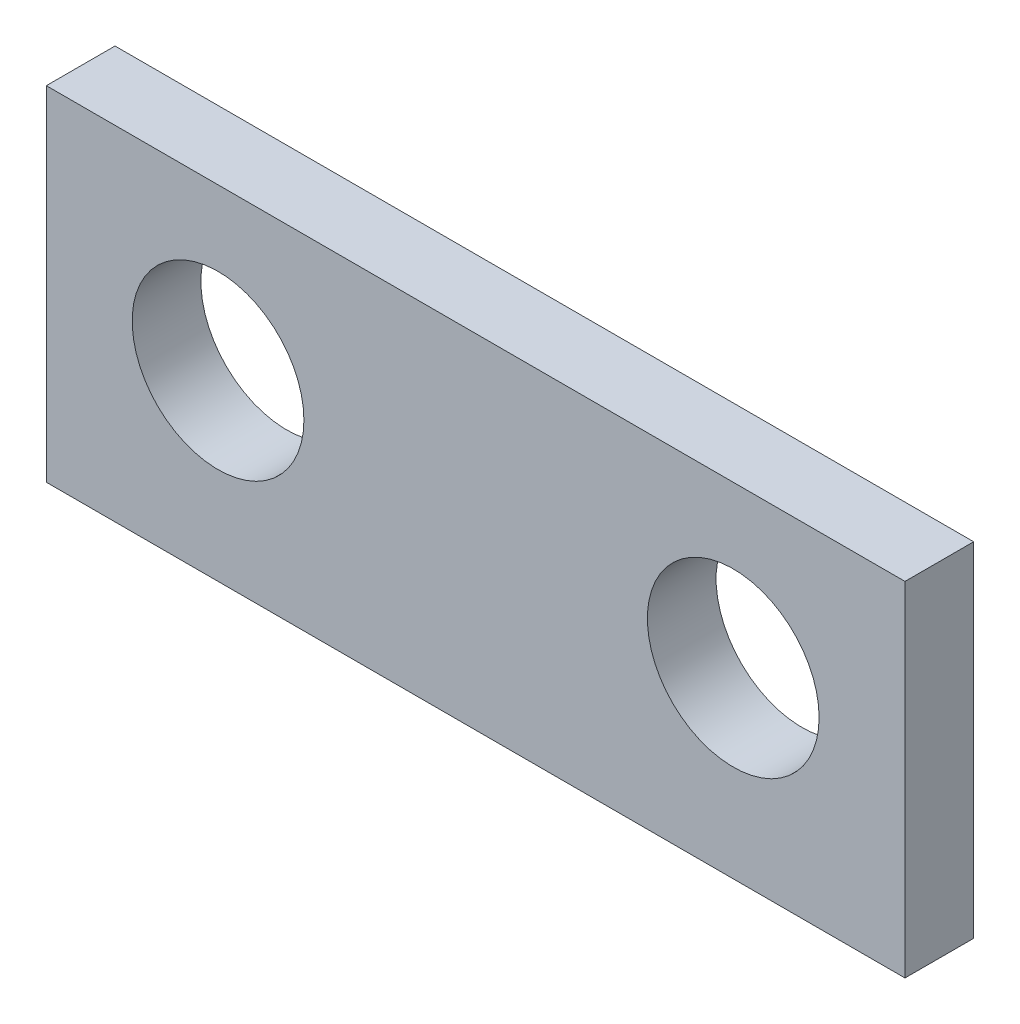
SolidWorks part; units mm, degrees
ref_plane "Front Plane" through (0, 0, 0) normal (0, 0, 1) x (1, 0, 0)
ref_plane "Top Plane" through (0, 0, 0) normal (0, 1, 0) x (1, 0, 0)
ref_plane "Right Plane" through (0, 0, 0) normal (1, 0, 0) x (0, 0, -1)
sketch "Sketch1" plane through (0, 0, 0) normal (0, 0, 1) x (1, 0, 0)
  line L0 (15.875, 12.7) -> (15.875, 0) construction
  line L1 (0, 0) -> (31.75, 0)
  line L2 (0, 0) -> (0, 12.7)
  line L3 (0, 12.7) -> (31.75, 12.7)
  line L4 (31.75, 0) -> (31.75, 12.7)
  circle A0 centre (6.35, 6.753) radius 3.175
  circle A1 centre (25.4, 6.753) radius 3.175
  dimension "D3" = 6.35
  dimension "D4" = 6.35
  dimension "D5" = 19.05
  dimension "D1" = 31.75
  dimension "D2" = 12.7
  dimension "D6" = 19.05
extrude "Boss-Extrude1" add sketch "Sketch1" along normal blind 2.54
